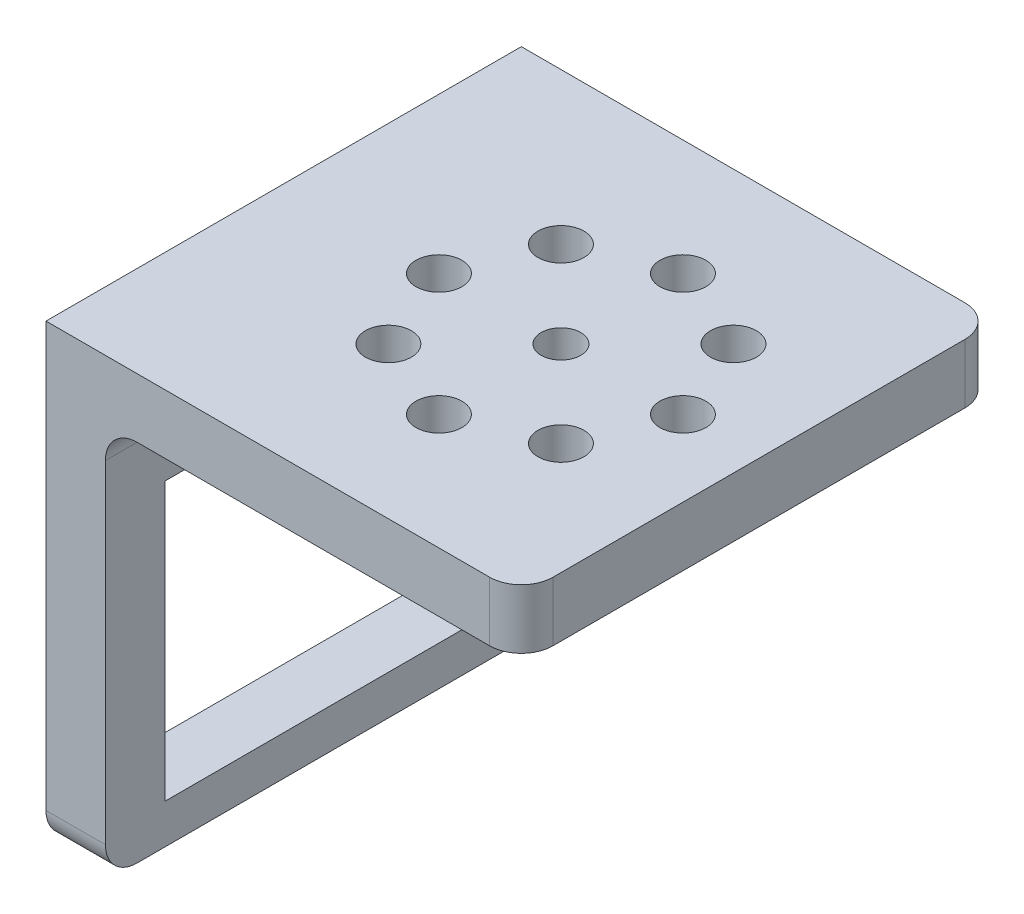
SolidWorks part; units mm, degrees
ref_plane "Front" through (0, 0, 0) normal (0, 0, 1) x (1, 0, 0)
ref_plane "Top" through (0, 0, 0) normal (0, 1, 0) x (1, 0, 0)
ref_plane "Right" through (0, 0, 0) normal (1, 0, 0) x (0, 0, -1)
sketch "Sketch1" plane through (0, 0, 0) normal (0, 0, 1) x (1, 0, 0)
  line L0 (0, 0) -> (0, 31.75)
  line L1 (0, 31.75) -> (33.3375, 31.75)
  line L2 (33.3375, 31.75) -> (33.3375, 36.5125)
  line L3 (33.3375, 36.5125) -> (-4.7625, 36.5125)
  line L4 (-4.7625, 36.5125) -> (-4.7625, 0)
  line L5 (-4.7625, 0) -> (0, 0)
  dimension "D1" = 4.7625
  dimension "D2" = 4.7625
  dimension "D3" = 31.75
  dimension "D4" = 38.1
extrude "Boss-Extrude1" add sketch "Sketch1" along normal blind 38.1
sketch "Sketch2" plane through (-4.7625, 0, 0) normal (-1, 0, 0) x (0, 0, 1)
  line L0 (38.1, 36.5125) -> (38.1, 0) construction
  line L1 (4.7625, 25.4) -> (33.3375, 25.4)
  line L2 (4.7625, 25.4) -> (4.7625, 3.175)
  line L3 (4.7625, 3.175) -> (33.3375, 3.175)
  line L4 (33.3375, 25.4) -> (33.3375, 3.175)
  line L5 (38.1, 0) -> (0, 0) construction
  dimension "D1" = 22.225
  dimension "D2" = 28.575
  dimension "D3" = 4.7625
  dimension "D4" = 3.175
extrude "Cut-Extrude1" cut sketch "Sketch2" against normal through all
sketch "Sketch3" plane through (0, 36.5125, 0) normal (0, 1, 0) x (1, 0, 0)
  line L0 (33.3375, 0) -> (-4.7625, 0) construction
  line L1 (33.3375, -38.1) -> (33.3375, 0) construction
  circle A0 centre (17.4625, -19.05) radius 1.5875
  dimension "D1" = 3.175
  dimension "D2" = 19.05
  dimension "D3" = 15.875
extrude "Cut-Extrude2" cut sketch "Sketch3" against normal through all
sketch "Sketch4" plane through (0, 36.5125, 0) normal (0, 1, 0) x (1, 0, 0)
  line L0 (33.3375, -38.1) -> (33.3375, 0) construction
  circle A0 centre (27.2415, -19.05) radius 1.8415
  circle A1 centre (17.4625, -19.05) radius 1.5875 construction
  point P6 (33.3375, -19.05)
  dimension "D1" = 3.683
  dimension "D2" = 9.779
extrude "Cut-Extrude3" cut sketch "Sketch4" against normal through all
pattern_circular "CirPattern1" count 8 over 360 about axis through (17.4625, 0, 19.05) along (0, 1, 0) of "Cut-Extrude3"
fillet "Fillet1" radius 2.54 1 edges at (0, 31.75, 19.05)
fillet "Fillet2" radius 2.54 4 edges at (33.3375, 34.1313, 0) (33.3375, 34.1313, 38.1) (-2.3813, 0, 38.1) (-2.3813, 0, 0)
